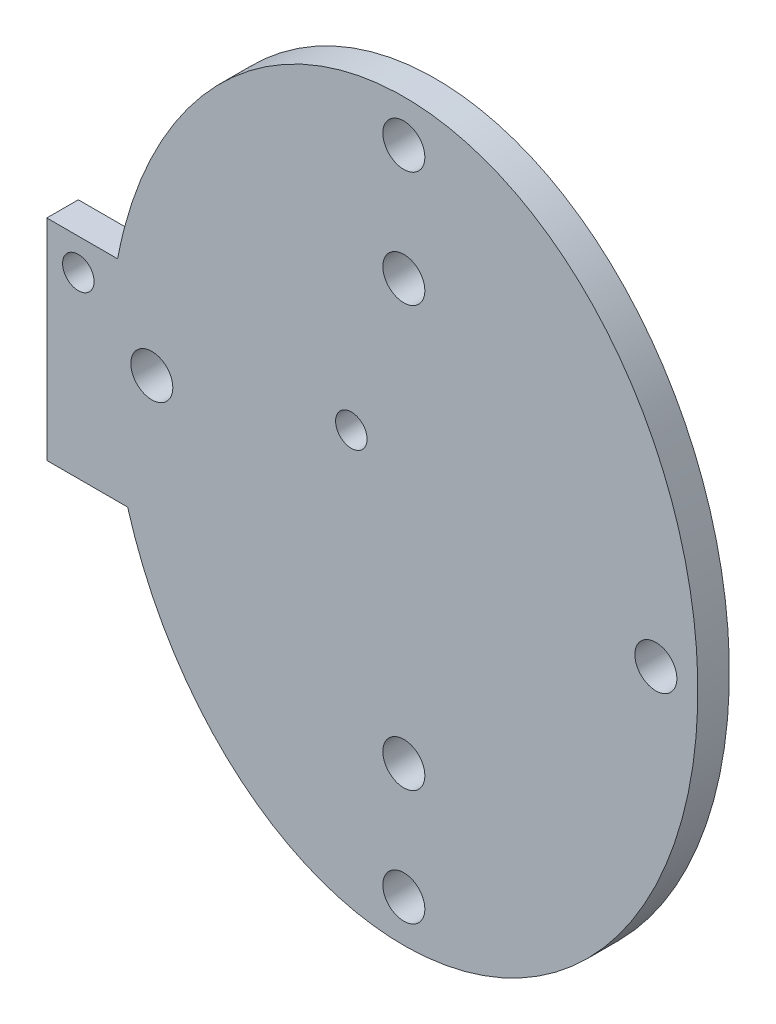
SolidWorks part; units mm, degrees
material "Balsa"
ref_plane "Plan de face" through (0, 0, 0) normal (0, 0, 1) x (1, 0, 0)
ref_plane "Plan de dessus" through (0, 0, 0) normal (0, 1, 0) x (1, 0, 0)
ref_plane "Plan de droite" through (0, 0, 0) normal (1, 0, 0) x (0, 0, -1)
sketch "Esquisse1" plane through (0, 0, 0) normal (0, 0, 1) x (1, 0, 0)
  circle A0 centre (0, 20) radius 2
  circle A1 centre (0, -20) radius 2
  ellipse E0 centre (0, 0) end of major axis (0, 35) minor radius 28
  dimension "D1" = 4
  dimension "D4" = 4
  dimension "D2" = 20
  dimension "D3" = 20
extrude "Boss.-Extru.1" add sketch "Esquisse1" along normal blind 3
sketch "Esquisse2" plane through (0, 0, 0) normal (0, 0, -1) x (-1, 0, 0)
  circle A0 centre (24, 0) radius 2
  circle A1 centre (-24, 0) radius 2
  circle A2 centre (0, 31) radius 2
  circle A3 centre (0, -31) radius 2
  dimension "D1" = 4
  dimension "D2" = 4
  dimension "D3" = 4
  dimension "D4" = 4
  dimension "D5" = 24
  dimension "D6" = 31
  dimension "D7" = 24
  dimension "D8" = 31
extrude "Enlèv. mat.-Extru.1" cut sketch "Esquisse2" against normal blind 10
sketch "Esquisse4" plane through (0, 0, 0) normal (0, 0, -1) x (-1, 0, 0)
  line L1 (26, 8) -> (34, 8)
  line L2 (26, 8) -> (26, -12)
  line L3 (26, -12) -> (34, -12)
  line L4 (34, 8) -> (34, -12)
  dimension "D1" = 20
  dimension "D2" = 8
  dimension "D3" = 8
  dimension "D4" = 26
extrude "Boss.-Extru.2" add sketch "Esquisse4" against normal blind 3
sketch "Esquisse3" plane through (0, 0, 0) normal (0, 0, -1) x (-1, 0, 0)
  circle A0 centre (5, 5) radius 1.5
  circle A1 centre (31, 5) radius 1.5
  dimension "D1" = 3
  dimension "D2" = 3
  dimension "D3" = 5
  dimension "D4" = 5
  dimension "D5" = 26
  dimension "D6" = 5
extrude "Enlèv. mat.-Extru.2" cut sketch "Esquisse3" against normal blind 10
